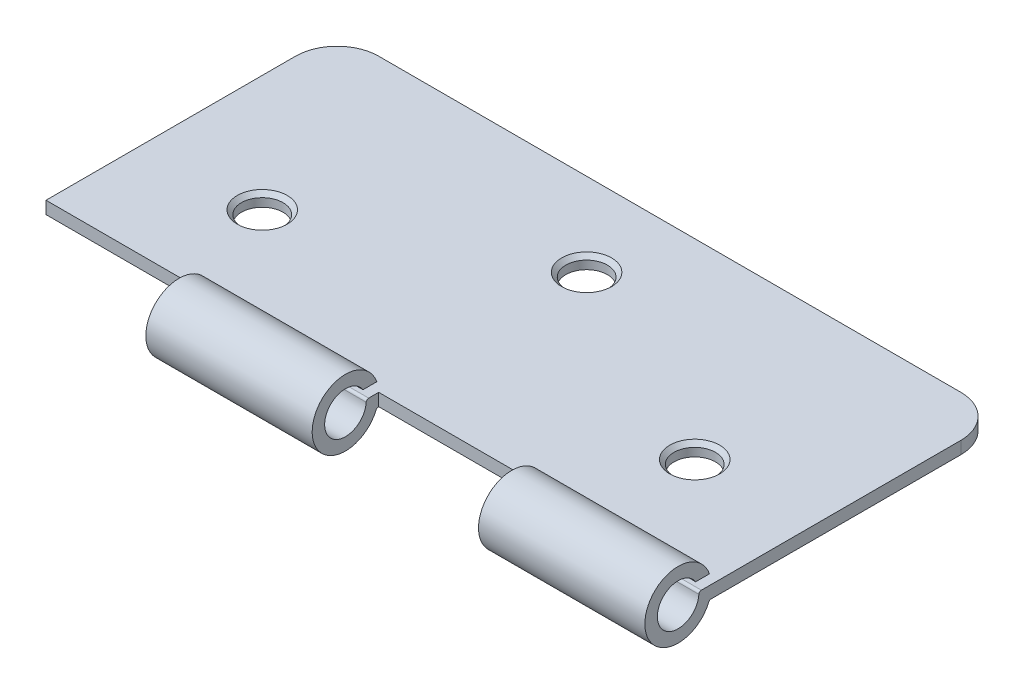
SolidWorks part; units mm, degrees
ref_plane "Front Plane" through (0, 0, 0) normal (0, 0, 1) x (1, 0, 0)
ref_plane "Top Plane" through (0, 0, 0) normal (0, 1, 0) x (1, 0, 0)
ref_plane "Right Plane" through (0, 0, 0) normal (1, 0, 0) x (0, 0, -1)
sketch "Sketch1" plane through (0, 0, 0) normal (0, 1, 0) x (1, 0, 0)
  line L1 (40, -17.5) -> (-40, -17.5)
  line L2 (40, -17.5) -> (40, 12.5)
  line L3 (35, 17.5) -> (-35, 17.5)
  line L4 (-40, -17.5) -> (-40, 12.5)
  line L5 (40, -17.5) -> (-40, 17.5) construction
  line L6 (40, 17.5) -> (-40, -17.5) construction
  arc A0 (40, 12.5) -> (35, 17.5) centre (35, 12.5) ccw
  arc A1 (-35, 17.5) -> (-40, 12.5) centre (-35, 12.5) ccw
  point P0 (0, 0)
  dimension "D3" = 5
  dimension "D1" = 80
  dimension "D2" = 35
extrude "Boss-Extrude1" add sketch "Sketch1" along normal blind 1.5
sketch "Sketch3" plane through (40, 0, 0) normal (1, 0, 0) x (0, 0, -1)
  line L0 (-19.3859, 2.7127) -> (-17.7283, 2.7127)
  line L1 (-17.5, 0) -> (-17.5315, 0.0006)
  line L2 (-17.5, 0) -> (-17.5, 1.5)
  line L3 (-17.5, 1.5) -> (-18.7035, 1.5)
  arc A0 (-17.7283, 2.7127) -> (-17.8138, -0.1825) centre (-21.4981, 1.3752) ccw
  arc A1 (-19.3859, 2.7127) -> (-19.0029, 1.2188) centre (-21.4981, 1.3752) ccw
  arc A2 (-17.5, 1.2504) -> (-17.5, 1.5) centre (-21.4981, 1.3752) ccw
  arc A3 (-17.5315, 0.0006) -> (-17.8138, -0.1825) centre (-17.5375, -0.2993) ccw
  arc A4 (-18.7035, 1.5) -> (-19.0029, 1.2188) centre (-18.7035, 1.2) ccw
  dimension "D1" = 8
  dimension "D2" = 5
  dimension "D3" = 0.3
extrude "Boss-Extrude2" add sketch "Sketch3" against normal blind 20 contours L3 A4 A1 L0 A0 A3 L1 L2
pattern_linear "LPattern1" count 2 spacing 40 along (-1, 0, 0) of "Boss-Extrude2"
sketch "Sketch4" plane through (0, 1.5, 0) normal (0, 1, 0) x (1, 0, 0)
  line L0 (0, -17.5) -> (20, -17.5) construction
  line L1 (40, -18.7035) -> (40, 12.5) construction
  line L2 (-40, 12.5) -> (-40, -17.5) construction
  line L3 (-40, -17.5) -> (-20, -17.5) construction
  line L4 (35, 17.5) -> (-35, 17.5) construction
  circle A0 centre (0, 7.5) radius 2.5
  circle A1 centre (-26, -5.5) radius 2.5
  circle A2 centre (26, -5.5) radius 2.5
  dimension "D1" = 5
  dimension "D2" = 5
  dimension "D3" = 5
  dimension "D4" = 12
  dimension "D5" = 14
  dimension "D6" = 14
  dimension "D7" = 12
  dimension "D8" = 10
extrude "Cut-Extrude1" cut sketch "Sketch4" against normal through all
chamfer "Chamfer1" distance 0.5 angle 45 3 edges at (26, 1.5, 8) (0, 1.5, -5) (-26, 1.5, 8)
